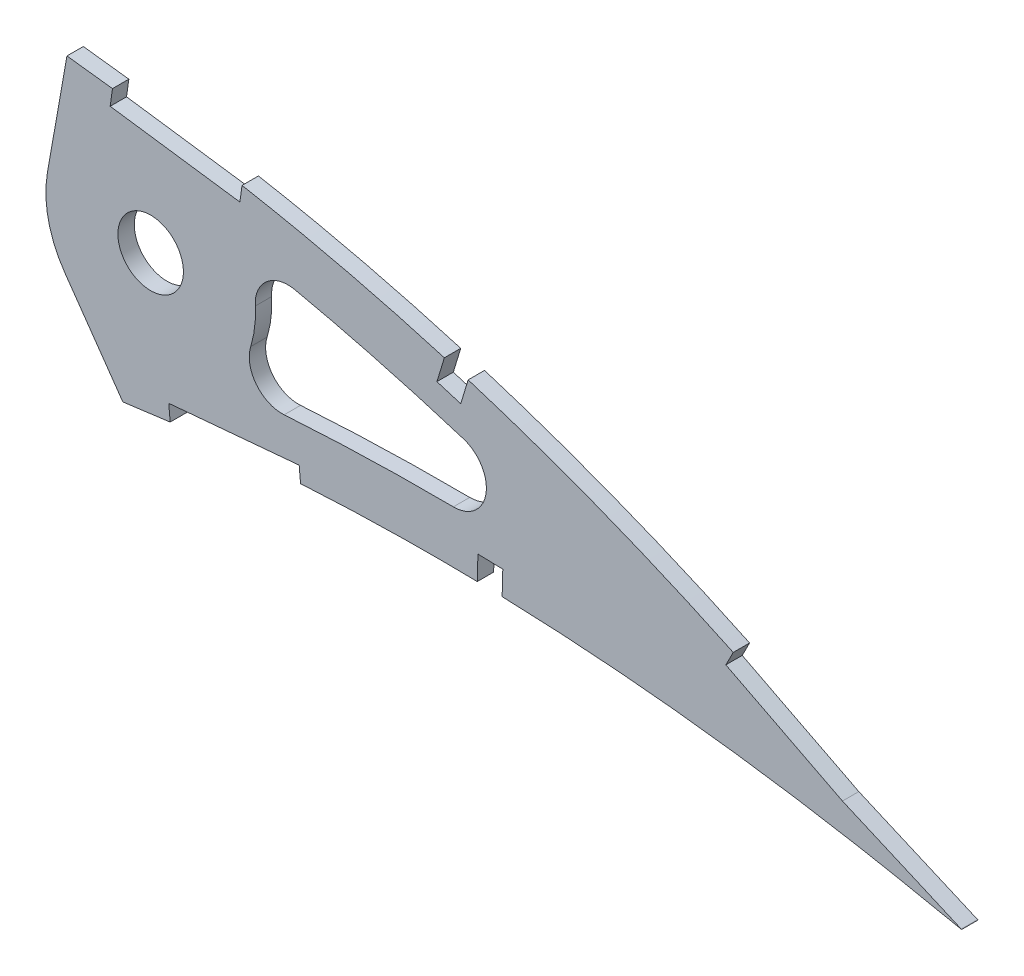
SolidWorks part; units mm, degrees
material "Plywood"
ref_plane "Front Plane" through (0, 0, 0) normal (0, 0, 1) x (1, 0, 0)
ref_plane "Top Plane" through (0, 0, 0) normal (0, 1, 0) x (1, 0, 0)
ref_plane "Right Plane" through (0, 0, 0) normal (1, 0, 0) x (0, 0, -1)
curve "Curve2"
  spline degree 3 poles (520.229, 0.8111, 0) (520.1892, 0.8357, 0) (520.0299, 0.9341, 0) (519.6711, 1.1542, 0) (519.0735, 1.5208, 0) (518.237, 2.0313, 0) (517.1622, 2.6844, 0) (515.8486, 3.4756, 0) (514.2969, 4.4021, 0) (512.5075, 5.4598, 0) (510.4807, 6.6436, 0) (508.2172, 7.9486, 0) (505.7172, 9.3676, 0) (502.9816, 10.8948, 0) (500.0114, 12.5227, 0) (496.8072, 14.2443, 0) (493.3701, 16.0505, 0) (489.7015, 17.9338, 0) (485.8019, 19.8836, 0) (481.6733, 21.8919, 0) (477.317, 23.9487, 0) (472.7345, 26.0429, 0) (467.9284, 28.1661, 0) (462.9001, 30.305, 0) (457.6524, 32.4505, 0) (452.1876, 34.5902, 0) (446.5089, 36.7144, 0) (440.6184, 38.8094, 0) (434.5207, 40.866, 0) (428.2186, 42.8708, 0) (421.7166, 44.813, 0) (415.0186, 46.68, 0) (408.1302, 48.4622, 0) (401.0555, 50.1466, 0) (393.8008, 51.7219, 0) (386.3718, 53.1787, 0) (378.7746, 54.5024, 0) (371.0303, 55.692, 0) (363.2636, 56.6815, 0) (355.5128, 57.652, 0) (347.7736, 58.5637, 0) (339.9398, 59.4368, 0) (332.019, 60.2663, 0) (324.019, 61.0497, 0) (315.9478, 61.7836, 0) (307.814, 62.4658, 0) (299.6253, 63.0925, 0) (291.3904, 63.6628, 0) (283.1174, 64.1714, 0) (274.8152, 64.6183, 0) (266.4922, 65.0001, 0) (258.157, 65.3142, 0) (249.8185, 65.5589, 0) (241.4854, 65.7316, 0) (233.1666, 65.8314, 0) (224.8708, 65.8555, 0) (216.6071, 65.8035, 0) (208.384, 65.6736, 0) (200.2107, 65.464, 0) (192.0958, 65.1743, 0) (184.048, 64.8046, 0) (176.0762, 64.3519, 0) (168.189, 63.8191, 0) (160.3952, 63.2038, 0) (152.7034, 62.506, 0) (145.1216, 61.7286, 0) (137.6583, 60.8693, 0) (130.3214, 59.9308, 0) (123.1191, 58.9147, 0) (116.0593, 57.8206, 0) (109.1496, 56.6517, 0) (102.3976, 55.409, 0) (95.8102, 54.0963, 0) (89.3948, 52.714, 0) (83.1581, 51.266, 0) (77.1065, 49.7551, 0) (71.2467, 48.1838, 0) (65.5845, 46.5561, 0) (60.1256, 44.8756, 0) (54.8764, 43.1442, 0) (49.8409, 41.3683, 0) (45.0253, 39.5493, 0) (40.4333, 37.6928, 0) (36.0702, 35.8014, 0) (31.9393, 33.8806, 0) (28.0452, 31.9329, 0) (24.3908, 29.9636, 0) (20.9797, 27.9757, 0) (17.8153, 25.973, 0) (14.8987, 23.9604, 0) (12.2341, 21.9394, 0) (9.8224, 19.9149, 0) (7.6651, 17.8901, 0) (5.7652, 15.8664, 0) (4.1228, 13.8473, 0) (2.7399, 11.8344, 0) (1.6168, 9.8297, 0) (0.7561, 7.8345, 0) (0.1568, 5.85, 0) (-0.1712, 3.8792, 0) (-0.2528, 1.9205, 0) (-0.0842, 0.6392, 0) (0, 0, 0) knots 0 0 0 0 0.000254 0.001015 0.002283 0.004057 0.006331 0.009105 0.012374 0.016134 0.02038 0.025106 0.030306 0.035972 0.0421 0.048678 0.055702 0.06316 0.071046 0.07935 0.088063 0.097176 0.106678 0.116562 0.126814 0.137428 0.148394 0.1597 0.171338 0.183298 0.19557 0.208144 0.221012 0.234162 0.247587 0.261277 0.275223 0.289414 0.303771 0.317689 0.331784 0.34604 0.360444 0.374983 0.38964 0.404403 0.419257 0.434187 0.449177 0.464215 0.479284 0.49437 0.509458 0.524532 0.539579 0.554583 0.56953 0.584403 0.599191 0.613877 0.628447 0.642889 0.657186 0.671326 0.685294 0.699078 0.712665 0.726043 0.739198 0.752118 0.764792 0.777208 0.789356 0.801224 0.812804 0.824083 0.835055 0.84571 0.856038 0.866034 0.875689 0.884998 0.893953 0.902553 0.910789 0.918661 0.926166 0.933303 0.940071 0.946475 0.952518 0.958205 0.963547 0.968557 0.97325 0.977651 0.981787 0.985694 0.989415 0.993001 0.996508 1 1 1 1
curve "Curve3"
  spline degree 3 poles (0, 0, 0) (0.1336, -0.6306, 0) (0.4014, -1.8948, 0) (1.129, -3.7148, 0) (2.0912, -5.4642, 0) (3.3081, -7.1386, 0) (4.7718, -8.7374, 0) (6.479, -10.2623, 0) (8.428, -11.7125, 0) (10.6162, -13.0874, 0) (13.0406, -14.3883, 0) (15.6982, -15.6145, 0) (18.5868, -16.7656, 0) (21.7032, -17.8401, 0) (25.0435, -18.8396, 0) (28.6046, -19.7616, 0) (32.3825, -20.6074, 0) (36.3735, -21.375, 0) (40.5732, -22.065, 0) (44.9774, -22.6771, 0) (49.5814, -23.2117, 0) (54.3808, -23.6676, 0) (59.3708, -24.0458, 0) (64.5464, -24.3466, 0) (69.9027, -24.5709, 0) (75.4344, -24.718, 0) (81.1363, -24.7899, 0) (87.003, -24.788, 0) (93.0289, -24.7115, 0) (99.2088, -24.5648, 0) (105.5368, -24.3469, 0) (112.0073, -24.0604, 0) (118.6142, -23.7083, 0) (125.3518, -23.2917, 0) (132.2141, -22.8125, 0) (139.1951, -22.2745, 0) (146.2885, -21.679, 0) (153.4882, -21.0296, 0) (160.7876, -20.3295, 0) (168.1806, -19.5808, 0) (175.6606, -18.7872, 0) (183.2209, -17.9512, 0) (190.8551, -17.0772, 0) (198.5563, -16.1668, 0) (206.3179, -15.2253, 0) (214.1326, -14.2544, 0) (221.9939, -13.2579, 0) (229.8947, -12.2404, 0) (237.8276, -11.2019, 0) (245.786, -10.1497, 0) (253.7621, -9.0829, 0) (261.7491, -8.0072, 0) (269.7395, -6.9257, 0) (277.7256, -5.8389, 0) (285.7003, -4.7513, 0) (293.6562, -3.6657, 0) (301.5856, -2.5824, 0) (309.4812, -1.5067, 0) (317.3352, -0.4385, 0) (325.1402, 0.6201, 0) (332.8888, 1.6659, 0) (340.5737, 2.6975, 0) (348.187, 3.7144, 0) (355.721, 4.7168, 0) (363.0553, 5.6745, 0) (370.1707, 6.6383, 0) (377.0913, 7.4284, 0) (383.9258, 8.1028, 0) (390.6811, 8.6557, 0) (397.3493, 9.0951, 0) (403.9227, 9.4241, 0) (410.3934, 9.6473, 0) (416.7532, 9.7713, 0) (422.9943, 9.7993, 0) (429.1081, 9.7402, 0) (435.0867, 9.5987, 0) (440.9216, 9.3813, 0) (446.6049, 9.0952, 0) (452.1283, 8.7483, 0) (457.4837, 8.3456, 0) (462.6634, 7.8966, 0) (467.6597, 7.4078, 0) (472.4647, 6.8849, 0) (477.0715, 6.3387, 0) (481.4727, 5.7729, 0) (485.6616, 5.1968, 0) (489.6316, 4.6162, 0) (493.3764, 4.0385, 0) (496.89, 3.4693, 0) (500.1667, 2.916, 0) (503.2016, 2.384, 0) (505.9892, 1.8782, 0) (508.5257, 1.4052, 0) (510.8062, 0.9673, 0) (512.8275, 0.5717, 0) (514.5859, 0.2202, 0) (516.0789, -0.0824, 0) (517.3037, -0.3347, 0) (518.2586, -0.5328, 0) (518.9417, -0.6767, 0) (519.3522, -0.7624, 0) (519.5346, -0.8013, 0) (519.5802, -0.8111, 0) knots 0 0 0 0 0.003638 0.007293 0.011028 0.014901 0.018963 0.023258 0.027821 0.032679 0.037853 0.043362 0.049215 0.055422 0.061989 0.068918 0.076211 0.083868 0.091887 0.100266 0.109 0.118085 0.127515 0.137285 0.147388 0.157816 0.168563 0.179619 0.190977 0.202627 0.21456 0.226767 0.239236 0.251959 0.264924 0.27812 0.291536 0.30516 0.318981 0.332985 0.347163 0.361499 0.375981 0.390597 0.405333 0.420175 0.43511 0.450124 0.465203 0.480333 0.495501 0.51069 0.525887 0.541078 0.556247 0.571382 0.586466 0.601485 0.616424 0.631269 0.646007 0.660621 0.675098 0.689423 0.703582 0.716908 0.730009 0.742952 0.755726 0.76832 0.780724 0.792927 0.804916 0.816679 0.828204 0.839475 0.850481 0.861208 0.871639 0.881763 0.891564 0.901027 0.910139 0.918884 0.927249 0.935221 0.942785 0.949928 0.956638 0.962904 0.968712 0.974054 0.978918 0.983297 0.98718 0.990561 0.993433 0.995791 0.99763 0.998946 0.999737 1 1 1 1
sketch "Sketch1" plane through (0, 0, 0) normal (0, 0, 1) x (1, 0, 0)
  line L1 (519.5802, -0.8111) -> (524.4049, -1.7687)
  line L2 (520.229, 0.8111) -> (524.4049, -1.7687)
  spline S0 degree 3 poles (-2903.7635, -749.124) (66.2436, 68.8235) (-8.6937, 20.855) (1.129, -3.7148) (2.0912, -5.4642) (3.3081, -7.1386) (4.7718, -8.7374) (6.479, -10.2623) (8.428, -11.7125) (10.6162, -13.0874) (13.0406, -14.3883) (15.6982, -15.6145) (18.5868, -16.7656) (21.7032, -17.8401) (25.0435, -18.8396) (28.6046, -19.7616) (32.3825, -20.6074) (36.3735, -21.375) (40.5732, -22.065) (44.9774, -22.6771) (49.5814, -23.2117) (54.3808, -23.6676) (59.3708, -24.0458) (64.5464, -24.3466) (69.9027, -24.5709) (75.4344, -24.718) (81.1363, -24.7899) (87.003, -24.788) (93.0289, -24.7115) (99.2088, -24.5648) (105.5368, -24.3469) (112.0073, -24.0604) (118.6142, -23.7083) (125.3518, -23.2917) (132.2141, -22.8125) (139.1951, -22.2745) (146.2885, -21.679) (153.4882, -21.0296) (160.7876, -20.3295) (168.1806, -19.5808) (175.6606, -18.7872) (183.2209, -17.9512) (190.8551, -17.0772) (198.5563, -16.1668) (206.3179, -15.2253) (214.1326, -14.2544) (221.9939, -13.2579) (229.8947, -12.2404) (237.8276, -11.2019) (245.786, -10.1497) (253.7621, -9.0829) (261.7491, -8.0072) (269.7395, -6.9257) (277.7256, -5.8389) (285.7003, -4.7513) (293.6562, -3.6657) (301.5856, -2.5824) (309.4812, -1.5067) (317.3352, -0.4385) (325.1402, 0.6201) (332.8888, 1.6659) (340.5737, 2.6975) (348.187, 3.7144) (355.721, 4.7168) (363.0553, 5.6745) (370.1707, 6.6383) (377.0913, 7.4284) (383.9258, 8.1028) (390.6811, 8.6557) (397.3493, 9.0951) (403.9227, 9.4241) (410.3934, 9.6473) (416.7532, 9.7713) (422.9943, 9.7993) (429.1081, 9.7402) (435.0867, 9.5987) (440.9216, 9.3813) (446.6049, 9.0952) (452.1283, 8.7483) (457.4837, 8.3456) (462.6634, 7.8966) (467.6597, 7.4078) (472.4647, 6.8849) (477.0715, 6.3387) (481.4727, 5.7729) (485.6616, 5.1968) (489.6316, 4.6162) (493.3764, 4.0385) (496.89, 3.4693) (500.1667, 2.916) (503.2016, 2.384) (505.9892, 1.8782) (508.5257, 1.4052) (510.8062, 0.9673) (512.8275, 0.5717) (514.5859, 0.2202) (516.0789, -0.0824) (517.3037, -0.3347) (518.2586, -0.5328) (518.9417, -0.6767) (537.0698, -4.4604) (553.3394, -15.9066) (1193.1482, 2921.6684) knots -0.137857 -0.137857 -0.137857 -0.137857 0.003638 0.007293 0.011028 0.014901 0.018963 0.023258 0.027821 0.032679 0.037853 0.043362 0.049215 0.055422 0.061989 0.068918 0.076211 0.083868 0.091887 0.100266 0.109 0.118085 0.127515 0.137285 0.147388 0.157816 0.168563 0.179619 0.190977 0.202627 0.21456 0.226767 0.239236 0.251959 0.264924 0.27812 0.291536 0.30516 0.318981 0.332985 0.347163 0.361499 0.375981 0.390597 0.405333 0.420175 0.43511 0.450124 0.465203 0.480333 0.495501 0.51069 0.525887 0.541078 0.556247 0.571382 0.586466 0.601485 0.616424 0.631269 0.646007 0.660621 0.675098 0.689423 0.703582 0.716908 0.730009 0.742952 0.755726 0.76832 0.780724 0.792927 0.804916 0.816679 0.828204 0.839475 0.850481 0.861208 0.871639 0.881763 0.891564 0.901027 0.910139 0.918884 0.927249 0.935221 0.942785 0.949928 0.956638 0.962904 0.968712 0.974054 0.978918 0.983297 0.98718 0.990561 0.993433 0.995791 0.99763 0.998946 0.999737 1.102307 1.102307 1.102307 1.102307 only from (0, 0) to (519.5802, -0.8111) construction
  spline S1 degree 3 poles (2144.5607, 2521.6799) (550.9976, -26.3511) (537.2872, -9.6513) (519.6711, 1.1542) (519.0735, 1.5208) (518.237, 2.0313) (517.1622, 2.6844) (515.8486, 3.4756) (514.2969, 4.4021) (512.5075, 5.4598) (510.4807, 6.6436) (508.2172, 7.9486) (505.7172, 9.3676) (502.9816, 10.8948) (500.0114, 12.5227) (496.8072, 14.2443) (493.3701, 16.0505) (489.7015, 17.9338) (485.8019, 19.8836) (481.6733, 21.8919) (477.317, 23.9487) (472.7345, 26.0429) (467.9284, 28.1661) (462.9001, 30.305) (457.6524, 32.4505) (452.1876, 34.5902) (446.5089, 36.7144) (440.6184, 38.8094) (434.5207, 40.866) (428.2186, 42.8708) (421.7166, 44.813) (415.0186, 46.68) (408.1302, 48.4622) (401.0555, 50.1466) (393.8008, 51.7219) (386.3718, 53.1787) (378.7746, 54.5024) (371.0303, 55.692) (363.2636, 56.6815) (355.5128, 57.652) (347.7736, 58.5637) (339.9398, 59.4368) (332.019, 60.2663) (324.019, 61.0497) (315.9478, 61.7836) (307.814, 62.4658) (299.6253, 63.0925) (291.3904, 63.6628) (283.1174, 64.1714) (274.8152, 64.6183) (266.4922, 65.0001) (258.157, 65.3142) (249.8185, 65.5589) (241.4854, 65.7316) (233.1666, 65.8314) (224.8708, 65.8555) (216.6071, 65.8035) (208.384, 65.6736) (200.2107, 65.464) (192.0958, 65.1743) (184.048, 64.8046) (176.0762, 64.3519) (168.189, 63.8191) (160.3952, 63.2038) (152.7034, 62.506) (145.1216, 61.7286) (137.6583, 60.8693) (130.3214, 59.9308) (123.1191, 58.9147) (116.0593, 57.8206) (109.1496, 56.6517) (102.3976, 55.409) (95.8102, 54.0963) (89.3948, 52.714) (83.1581, 51.266) (77.1065, 49.7551) (71.2467, 48.1838) (65.5845, 46.5561) (60.1256, 44.8756) (54.8764, 43.1442) (49.8409, 41.3683) (45.0253, 39.5493) (40.4333, 37.6928) (36.0702, 35.8014) (31.9393, 33.8806) (28.0452, 31.9329) (24.3908, 29.9636) (20.9797, 27.9757) (17.8153, 25.973) (14.8987, 23.9604) (12.2341, 21.9394) (9.8224, 19.9149) (7.6651, 17.8901) (5.7652, 15.8664) (4.1228, 13.8473) (2.7399, 11.8344) (1.6168, 9.8297) (0.7561, 7.8345) (0.1568, 5.85) (-0.1712, 3.8792) (-1.2714, -22.5145) (85.5395, -42.7616) (-2987.8188, -259.5241) knots -0.109813 -0.109813 -0.109813 -0.109813 0.000254 0.001015 0.002283 0.004057 0.006331 0.009105 0.012374 0.016134 0.02038 0.025106 0.030306 0.035972 0.0421 0.048678 0.055702 0.06316 0.071046 0.07935 0.088063 0.097176 0.106678 0.116562 0.126814 0.137428 0.148394 0.1597 0.171338 0.183298 0.19557 0.208144 0.221012 0.234162 0.247587 0.261277 0.275223 0.289414 0.303771 0.317689 0.331784 0.34604 0.360444 0.374983 0.38964 0.404403 0.419257 0.434187 0.449177 0.464215 0.479284 0.49437 0.509458 0.524532 0.539579 0.554583 0.56953 0.584403 0.599191 0.613877 0.628447 0.642889 0.657186 0.671326 0.685294 0.699078 0.712665 0.726043 0.739198 0.752118 0.764792 0.777208 0.789356 0.801224 0.812804 0.824083 0.835055 0.84571 0.856038 0.866034 0.875689 0.884998 0.893953 0.902553 0.910789 0.918661 0.926166 0.933303 0.940071 0.946475 0.952518 0.958205 0.963547 0.968557 0.97325 0.977651 0.981787 0.985694 0.989415 0.993001 0.996508 1.132043 1.132043 1.132043 1.132043 only from (520.229, 0.8111) to (0, 0) construction
  spline S2 degree 3 poles (0, 0) (0.1336, -0.6306) (0.4014, -1.8948) (1.129, -3.7148) (2.0912, -5.4642) (3.3081, -7.1386) (4.7718, -8.7374) (6.479, -10.2623) (8.428, -11.7125) (10.6162, -13.0874) (13.0406, -14.3883) (15.6982, -15.6145) (18.5868, -16.7656) (21.7032, -17.8401) (25.0435, -18.8396) (28.6046, -19.7616) (32.3825, -20.6074) (36.3735, -21.375) (40.5732, -22.065) (44.9774, -22.6771) (49.5814, -23.2117) (54.3808, -23.6676) (59.3708, -24.0458) (64.5464, -24.3466) (69.9027, -24.5709) (75.4344, -24.718) (81.1363, -24.7899) (87.003, -24.788) (93.0289, -24.7115) (99.2088, -24.5648) (105.5368, -24.3469) (112.0073, -24.0604) (118.6142, -23.7083) (125.3518, -23.2917) (132.2141, -22.8125) (139.1951, -22.2745) (146.2885, -21.679) (153.4882, -21.0296) (160.7876, -20.3295) (168.1806, -19.5808) (175.6606, -18.7872) (183.2209, -17.9512) (190.8551, -17.0772) (198.5563, -16.1668) (206.3179, -15.2253) (214.1326, -14.2544) (221.9939, -13.2579) (229.8947, -12.2404) (237.8276, -11.2019) (245.786, -10.1497) (253.7621, -9.0829) (261.7491, -8.0072) (269.7395, -6.9257) (277.7256, -5.8389) (285.7003, -4.7513) (293.6562, -3.6657) (301.5856, -2.5824) (309.4812, -1.5067) (317.3352, -0.4385) (325.1402, 0.6201) (332.8888, 1.6659) (340.5737, 2.6975) (348.187, 3.7144) (355.721, 4.7168) (363.0553, 5.6745) (370.1707, 6.6383) (377.0913, 7.4284) (383.9258, 8.1028) (390.6811, 8.6557) (397.3493, 9.0951) (403.9227, 9.4241) (410.3934, 9.6473) (416.7532, 9.7713) (422.9943, 9.7993) (429.1081, 9.7402) (435.0867, 9.5987) (440.9216, 9.3813) (446.6049, 9.0952) (452.1283, 8.7483) (457.4837, 8.3456) (462.6634, 7.8966) (467.6597, 7.4078) (472.4647, 6.8849) (477.0715, 6.3387) (481.4727, 5.7729) (485.6616, 5.1968) (489.6316, 4.6162) (493.3764, 4.0385) (496.89, 3.4693) (500.1667, 2.916) (503.2016, 2.384) (505.9892, 1.8782) (508.5257, 1.4052) (510.8062, 0.9673) (512.8275, 0.5717) (514.5859, 0.2202) (516.0789, -0.0824) (517.3037, -0.3347) (518.2586, -0.5328) (518.9417, -0.6767) (519.3522, -0.7624) (519.5346, -0.8013) (519.5802, -0.8111) knots 0 0 0 0 0.003638 0.007293 0.011028 0.014901 0.018963 0.023258 0.027821 0.032679 0.037853 0.043362 0.049215 0.055422 0.061989 0.068918 0.076211 0.083868 0.091887 0.100266 0.109 0.118085 0.127515 0.137285 0.147388 0.157816 0.168563 0.179619 0.190977 0.202627 0.21456 0.226767 0.239236 0.251959 0.264924 0.27812 0.291536 0.30516 0.318981 0.332985 0.347163 0.361499 0.375981 0.390597 0.405333 0.420175 0.43511 0.450124 0.465203 0.480333 0.495501 0.51069 0.525887 0.541078 0.556247 0.571382 0.586466 0.601485 0.616424 0.631269 0.646007 0.660621 0.675098 0.689423 0.703582 0.716908 0.730009 0.742952 0.755726 0.76832 0.780724 0.792927 0.804916 0.816679 0.828204 0.839475 0.850481 0.861208 0.871639 0.881763 0.891564 0.901027 0.910139 0.918884 0.927249 0.935221 0.942785 0.949928 0.956638 0.962904 0.968712 0.974054 0.978918 0.983297 0.98718 0.990561 0.993433 0.995791 0.99763 0.998946 0.999737 1 1 1 1
  spline S3 degree 3 poles (520.229, 0.8111) (520.1892, 0.8357) (520.0299, 0.9341) (519.6711, 1.1542) (519.0735, 1.5208) (518.237, 2.0313) (517.1622, 2.6844) (515.8486, 3.4756) (514.2969, 4.4021) (512.5075, 5.4598) (510.4807, 6.6436) (508.2172, 7.9486) (505.7172, 9.3676) (502.9816, 10.8948) (500.0114, 12.5227) (496.8072, 14.2443) (493.3701, 16.0505) (489.7015, 17.9338) (485.8019, 19.8836) (481.6733, 21.8919) (477.317, 23.9487) (472.7345, 26.0429) (467.9284, 28.1661) (462.9001, 30.305) (457.6524, 32.4505) (452.1876, 34.5902) (446.5089, 36.7144) (440.6184, 38.8094) (434.5207, 40.866) (428.2186, 42.8708) (421.7166, 44.813) (415.0186, 46.68) (408.1302, 48.4622) (401.0555, 50.1466) (393.8008, 51.7219) (386.3718, 53.1787) (378.7746, 54.5024) (371.0303, 55.692) (363.2636, 56.6815) (355.5128, 57.652) (347.7736, 58.5637) (339.9398, 59.4368) (332.019, 60.2663) (324.019, 61.0497) (315.9478, 61.7836) (307.814, 62.4658) (299.6253, 63.0925) (291.3904, 63.6628) (283.1174, 64.1714) (274.8152, 64.6183) (266.4922, 65.0001) (258.157, 65.3142) (249.8185, 65.5589) (241.4854, 65.7316) (233.1666, 65.8314) (224.8708, 65.8555) (216.6071, 65.8035) (208.384, 65.6736) (200.2107, 65.464) (192.0958, 65.1743) (184.048, 64.8046) (176.0762, 64.3519) (168.189, 63.8191) (160.3952, 63.2038) (152.7034, 62.506) (145.1216, 61.7286) (137.6583, 60.8693) (130.3214, 59.9308) (123.1191, 58.9147) (116.0593, 57.8206) (109.1496, 56.6517) (102.3976, 55.409) (95.8102, 54.0963) (89.3948, 52.714) (83.1581, 51.266) (77.1065, 49.7551) (71.2467, 48.1838) (65.5845, 46.5561) (60.1256, 44.8756) (54.8764, 43.1442) (49.8409, 41.3683) (45.0253, 39.5493) (40.4333, 37.6928) (36.0702, 35.8014) (31.9393, 33.8806) (28.0452, 31.9329) (24.3908, 29.9636) (20.9797, 27.9757) (17.8153, 25.973) (14.8987, 23.9604) (12.2341, 21.9394) (9.8224, 19.9149) (7.6651, 17.8901) (5.7652, 15.8664) (4.1228, 13.8473) (2.7399, 11.8344) (1.6168, 9.8297) (0.7561, 7.8345) (0.1568, 5.85) (-0.1712, 3.8792) (-0.2528, 1.9205) (-0.0842, 0.6392) (0, 0) knots 0 0 0 0 0.000254 0.001015 0.002283 0.004057 0.006331 0.009105 0.012374 0.016134 0.02038 0.025106 0.030306 0.035972 0.0421 0.048678 0.055702 0.06316 0.071046 0.07935 0.088063 0.097176 0.106678 0.116562 0.126814 0.137428 0.148394 0.1597 0.171338 0.183298 0.19557 0.208144 0.221012 0.234162 0.247587 0.261277 0.275223 0.289414 0.303771 0.317689 0.331784 0.34604 0.360444 0.374983 0.38964 0.404403 0.419257 0.434187 0.449177 0.464215 0.479284 0.49437 0.509458 0.524532 0.539579 0.554583 0.56953 0.584403 0.599191 0.613877 0.628447 0.642889 0.657186 0.671326 0.685294 0.699078 0.712665 0.726043 0.739198 0.752118 0.764792 0.777208 0.789356 0.801224 0.812804 0.824083 0.835055 0.84571 0.856038 0.866034 0.875689 0.884998 0.893953 0.902553 0.910789 0.918661 0.926166 0.933303 0.940071 0.946475 0.952518 0.958205 0.963547 0.968557 0.97325 0.977651 0.981787 0.985694 0.989415 0.993001 0.996508 1 1 1 1
extrude "Boss-Extrude1" add sketch "Sketch1" along normal blind 3.175
sketch "Sketch4" plane through (0, 0, 0) normal (0, 0, -1) x (-1, 0, 0)
  line L0 (-347.1309, 36.7611) -> (-350.9097, 58.1919)
  line L1 (-350.497, 21.5775) -> (-361.7496, 5.5072)
  line L2 (-367.1422, 33.2326) -> (-406.863, 33.2326)
  circle A0 centre (-367.1422, 33.2326) radius 20.32
  circle A1 centre (-367.1422, 33.2326) radius 6.35
  spline S2 degree 3 poles (1939.7558, -484.7932) (-49.4812, 57.6608) (7.5449, 17.9816) (-1.129, -3.7148) (-2.0912, -5.4642) (-3.3081, -7.1386) (-4.7718, -8.7374) (-6.479, -10.2623) (-8.428, -11.7125) (-10.6162, -13.0874) (-13.0406, -14.3883) (-15.6982, -15.6145) (-18.5868, -16.7656) (-21.7032, -17.8401) (-25.0435, -18.8396) (-28.6046, -19.7616) (-32.3825, -20.6074) (-36.3735, -21.375) (-40.5732, -22.065) (-44.9774, -22.6771) (-49.5814, -23.2117) (-54.3808, -23.6676) (-59.3708, -24.0458) (-64.5464, -24.3466) (-69.9027, -24.5709) (-75.4344, -24.718) (-81.1363, -24.7899) (-87.003, -24.788) (-93.0289, -24.7115) (-99.2088, -24.5648) (-105.5368, -24.3469) (-112.0073, -24.0604) (-118.6142, -23.7083) (-125.3518, -23.2917) (-132.2141, -22.8125) (-139.1951, -22.2745) (-146.2885, -21.679) (-153.4882, -21.0296) (-160.7876, -20.3295) (-168.1806, -19.5808) (-175.6606, -18.7872) (-183.2209, -17.9512) (-190.8551, -17.0772) (-198.5563, -16.1668) (-206.3179, -15.2253) (-214.1326, -14.2544) (-221.9939, -13.2579) (-229.8947, -12.2404) (-237.8276, -11.2019) (-245.786, -10.1497) (-253.7621, -9.0829) (-261.7491, -8.0072) (-269.7395, -6.9257) (-277.7256, -5.8389) (-285.7003, -4.7513) (-293.6562, -3.6657) (-301.5856, -2.5824) (-309.4812, -1.5067) (-317.3352, -0.4385) (-325.1402, 0.6201) (-332.8888, 1.6659) (-340.5737, 2.6975) (-348.187, 3.7144) (-355.721, 4.7168) (-363.0553, 5.6745) (-370.1707, 6.6383) (-377.0913, 7.4284) (-383.9258, 8.1028) (-390.6811, 8.6557) (-397.3493, 9.0951) (-403.9227, 9.4241) (-410.3934, 9.6473) (-416.7532, 9.7713) (-422.9943, 9.7993) (-429.1081, 9.7402) (-435.0867, 9.5987) (-440.9216, 9.3813) (-446.6049, 9.0952) (-452.1283, 8.7483) (-457.4837, 8.3456) (-462.6634, 7.8966) (-467.6597, 7.4078) (-472.4647, 6.8849) (-477.0715, 6.3387) (-481.4727, 5.7729) (-485.6616, 5.1968) (-489.6316, 4.6162) (-493.3764, 4.0385) (-496.89, 3.4693) (-500.1667, 2.916) (-503.2016, 2.384) (-505.9892, 1.8782) (-508.5257, 1.4052) (-510.8062, 0.9673) (-512.8275, 0.5717) (-514.5859, 0.2202) (-516.0789, -0.0824) (-517.3037, -0.3347) (-518.2586, -0.5328) (-518.9417, -0.6767) (-534.8295, -3.9928) (-549.2415, -13.1623) (-979.5797, 1945.0117) knots -0.120445 -0.120445 -0.120445 -0.120445 0.003638 0.007293 0.011028 0.014901 0.018963 0.023258 0.027821 0.032679 0.037853 0.043362 0.049215 0.055422 0.061989 0.068918 0.076211 0.083868 0.091887 0.100266 0.109 0.118085 0.127515 0.137285 0.147388 0.157816 0.168563 0.179619 0.190977 0.202627 0.21456 0.226767 0.239236 0.251959 0.264924 0.27812 0.291536 0.30516 0.318981 0.332985 0.347163 0.361499 0.375981 0.390597 0.405333 0.420175 0.43511 0.450124 0.465203 0.480333 0.495501 0.51069 0.525887 0.541078 0.556247 0.571382 0.586466 0.601485 0.616424 0.631269 0.646007 0.660621 0.675098 0.689423 0.703582 0.716908 0.730009 0.742952 0.755726 0.76832 0.780724 0.792927 0.804916 0.816679 0.828204 0.839475 0.850481 0.861208 0.871639 0.881763 0.891564 0.901027 0.910139 0.918884 0.927249 0.935221 0.942785 0.949928 0.956638 0.962904 0.968712 0.974054 0.978918 0.983297 0.98718 0.990561 0.993433 0.995791 0.99763 0.998946 0.999737 1.089371 1.089371 1.089371 1.089371 only from (0, 0) to (-519.5802, -0.8111) construction
  spline S3 degree 3 poles (-1613.7482, 1674.6901) (-547.5042, -22.2613) (-535.1053, -8.313) (-519.6711, 1.1542) (-519.0735, 1.5208) (-518.237, 2.0313) (-517.1622, 2.6844) (-515.8486, 3.4756) (-514.2969, 4.4021) (-512.5075, 5.4598) (-510.4807, 6.6436) (-508.2172, 7.9486) (-505.7172, 9.3676) (-502.9816, 10.8948) (-500.0114, 12.5227) (-496.8072, 14.2443) (-493.3701, 16.0505) (-489.7015, 17.9338) (-485.8019, 19.8836) (-481.6733, 21.8919) (-477.317, 23.9487) (-472.7345, 26.0429) (-467.9284, 28.1661) (-462.9001, 30.305) (-457.6524, 32.4505) (-452.1876, 34.5902) (-446.5089, 36.7144) (-440.6184, 38.8094) (-434.5207, 40.866) (-428.2186, 42.8708) (-421.7166, 44.813) (-415.0186, 46.68) (-408.1302, 48.4622) (-401.0555, 50.1466) (-393.8008, 51.7219) (-386.3718, 53.1787) (-378.7746, 54.5024) (-371.0303, 55.692) (-363.2636, 56.6815) (-355.5128, 57.652) (-347.7736, 58.5637) (-339.9398, 59.4368) (-332.019, 60.2663) (-324.019, 61.0497) (-315.9478, 61.7836) (-307.814, 62.4658) (-299.6253, 63.0925) (-291.3904, 63.6628) (-283.1174, 64.1714) (-274.8152, 64.6183) (-266.4922, 65.0001) (-258.157, 65.3142) (-249.8185, 65.5589) (-241.4854, 65.7316) (-233.1666, 65.8314) (-224.8708, 65.8555) (-216.6071, 65.8035) (-208.384, 65.6736) (-200.2107, 65.464) (-192.0958, 65.1743) (-184.048, 64.8046) (-176.0762, 64.3519) (-168.189, 63.8191) (-160.3952, 63.2038) (-152.7034, 62.506) (-145.1216, 61.7286) (-137.6583, 60.8693) (-130.3214, 59.9308) (-123.1191, 58.9147) (-116.0593, 57.8206) (-109.1496, 56.6517) (-102.3976, 55.409) (-95.8102, 54.0963) (-89.3948, 52.714) (-83.1581, 51.266) (-77.1065, 49.7551) (-71.2467, 48.1838) (-65.5845, 46.5561) (-60.1256, 44.8756) (-54.8764, 43.1442) (-49.8409, 41.3683) (-45.0253, 39.5493) (-40.4333, 37.6928) (-36.0702, 35.8014) (-31.9393, 33.8806) (-28.0452, 31.9329) (-24.3908, 29.9636) (-20.9797, 27.9757) (-17.8153, 25.973) (-14.8987, 23.9604) (-12.2341, 21.9394) (-9.8224, 19.9149) (-7.6651, 17.8901) (-5.7652, 15.8664) (-4.1228, 13.8473) (-2.7399, 11.8344) (-1.6168, 9.8297) (-0.7561, 7.8345) (-0.1568, 5.85) (0.1712, 3.8792) (1.1427, -19.4272) (-65.9725, -37.8239) (1990.4087, -188.0581) knots -0.095928 -0.095928 -0.095928 -0.095928 0.000254 0.001015 0.002283 0.004057 0.006331 0.009105 0.012374 0.016134 0.02038 0.025106 0.030306 0.035972 0.0421 0.048678 0.055702 0.06316 0.071046 0.07935 0.088063 0.097176 0.106678 0.116562 0.126814 0.137428 0.148394 0.1597 0.171338 0.183298 0.19557 0.208144 0.221012 0.234162 0.247587 0.261277 0.275223 0.289414 0.303771 0.317689 0.331784 0.34604 0.360444 0.374983 0.38964 0.404403 0.419257 0.434187 0.449177 0.464215 0.479284 0.49437 0.509458 0.524532 0.539579 0.554583 0.56953 0.584403 0.599191 0.613877 0.628447 0.642889 0.657186 0.671326 0.685294 0.699078 0.712665 0.726043 0.739198 0.752118 0.764792 0.777208 0.789356 0.801224 0.812804 0.824083 0.835055 0.84571 0.856038 0.866034 0.875689 0.884998 0.893953 0.902553 0.910789 0.918661 0.926166 0.933303 0.940071 0.946475 0.952518 0.958205 0.963547 0.968557 0.97325 0.977651 0.981787 0.985694 0.989415 0.993001 0.996508 1.11536 1.11536 1.11536 1.11536 only from (-520.229, 0.8111) to (0, 0) construction
  spline S4 degree 3 poles (-1978.354, 2157.5892) (159.6529, 858.6126) (-7.0413, 13.2519) (-10.1565, 1.1414) (-10.167, 1.1042) (-10.1763, 1.0725) (-10.1781, 1.0668) (-10.1835, 1.0497) (-10.1867, 1.0399) (-10.2052, 0.985) (-10.2286, 0.9219) (-10.2791, 0.8017) (-10.2985, 0.7574) (-10.3426, 0.661) (-10.3676, 0.6085) (-10.4428, 0.4561) (-10.496, 0.3558) (-10.6081, 0.1584) (-10.6662, 0.0627) (-10.855, -0.2291) (-11.0064, -0.4384) (-11.5378, -1.0936) (-11.9971, -1.5677) (-13.099, -2.5256) (-13.7412, -3.01) (-15.1702, -3.9568) (-15.9588, -4.4208) (-17.636, -5.3094) (-18.5262, -5.7351) (-21.3094, -6.9503) (-23.3073, -7.6749) (-27.467, -8.9758) (-29.6229, -9.5497) (-34.0316, -10.5753) (-36.2795, -11.0252) (-40.839, -11.8243) (-43.1471, -12.1728) (-47.8035, -12.7862) (-50.1501, -13.0508) (-57.2292, -13.7373) (-62.003, -14.0541) (-71.5985, -14.4809) (-76.422, -14.5891) (-83.6816, -14.6324) (-86.1037, -14.6268) (-90.9551, -14.5789) (-93.3856, -14.5371) (-100.6793, -14.3647) (-105.548, -14.1854) (-120.1773, -13.4939) (-129.9476, -12.83) (-149.5009, -11.2301) (-159.287, -10.2936) (-178.863, -8.2392) (-188.6532, -7.1203) (-203.3458, -5.3542) (-208.2424, -4.7511) (-218.0387, -3.5207) (-222.9395, -2.8943) (-232.7359, -1.6243) (-237.6385, -0.9795) (-247.4393, 0.3202) (-252.3404, 0.9774) (-262.147, 2.2986) (-267.05, 2.9625) (-276.8577, 4.2964) (-281.7641, 4.9659) (-291.5768, 6.3047) (-296.4825, 6.9752) (-306.3007, 8.3142) (-311.2087, 8.9822) (-325.9378, 10.9826) (-335.766, 12.3068) (-348.0467, 13.9451) (-350.5039, 14.2725) (-354.1964, 14.7609) (-355.4285, 14.923) (-357.8843, 15.2457) (-359.1092, 15.4066) (-361.5526, 15.7296) (-362.7689, 15.8922) (-365.2348, 16.221) (-366.4798, 16.3859) (-368.3663, 16.6273) (-368.9995, 16.7068) (-371.53, 17.0174) (-373.424, 17.2342) (-377.8329, 17.7104) (-380.3527, 17.9617) (-385.4072, 18.4196) (-387.9354, 18.6255) (-395.5221, 19.1767) (-400.5883, 19.4552) (-408.19, 19.7386) (-410.7237, 19.8108) (-415.7936, 19.9113) (-418.3301, 19.9392) (-425.9339, 19.9566) (-431.0019, 19.8815) (-441.1324, 19.5579) (-446.1907, 19.3102) (-453.7725, 18.8139) (-456.2982, 18.6271) (-775.6257, -7.5609) (-1062.3017, -351.5368) (-2984.1092, -1609.9578) knots -0.216436 -0.216436 -0.216436 -0.216436 0.001953 0.001953 0.00293 0.00293 0.003418 0.003418 0.003906 0.003906 0.005859 0.005859 0.006836 0.006836 0.007813 0.007813 0.009766 0.009766 0.011719 0.011719 0.015625 0.015625 0.023438 0.023438 0.03125 0.03125 0.039063 0.039063 0.046875 0.046875 0.0625 0.0625 0.078125 0.078125 0.09375 0.09375 0.109375 0.109375 0.125 0.125 0.15625 0.15625 0.1875 0.1875 0.203125 0.203125 0.21875 0.21875 0.25 0.25 0.3125 0.3125 0.375 0.375 0.4375 0.4375 0.46875 0.46875 0.5 0.5 0.53125 0.53125 0.5625 0.5625 0.59375 0.59375 0.625 0.625 0.65625 0.65625 0.6875 0.6875 0.75 0.75 0.765625 0.765625 0.773438 0.773438 0.78125 0.78125 0.789063 0.789063 0.796875 0.796875 0.800781 0.800781 0.8125 0.8125 0.828125 0.828125 0.84375 0.84375 0.875 0.875 0.890625 0.890625 0.90625 0.90625 0.9375 0.9375 0.96875 0.96875 0.984375 0.984375 2.947098 2.947098 2.947098 2.947098 only from (-10.022, 1.7185) to (-466.3815, 17.739)
  spline S5 degree 3 poles (-2960.1923, -1647.6146) (-778.0163, -316.2747) (-661.2066, -63.7231) (-457.1185, 21.6971) (-454.7864, 22.6463) (-450.1039, 24.4978) (-447.7524, 25.4007) (-443.0352, 27.1579) (-440.669, 28.0121) (-428.7885, 32.1652) (-419.1573, 35.0991) (-404.5516, 38.8923) (-399.6593, 40.0545) (-392.2853, 41.6432) (-389.8214, 42.1473) (-384.8862, 43.1026) (-382.4148, 43.5535) (-377.456, 44.4051) (-374.9691, 44.8071) (-371.8706, 45.272) (-371.2512, 45.3631) (-370.0129, 45.5414) (-369.3949, 45.6283) (-367.531, 45.885) (-365.6514, 46.1331) (-363.7495, 46.3759) (-362.4766, 46.5374) (-361.8369, 46.6182) (-359.9197, 46.8599) (-358.6437, 47.0199) (-354.8218, 47.4941) (-352.2828, 47.8012) (-347.1922, 48.3982) (-344.6438, 48.6888) (-339.5477, 49.2537) (-336.9993, 49.5279) (-329.3512, 50.3256) (-324.2496, 50.8242) (-308.9368, 52.2174) (-298.7176, 53.0107) (-278.2717, 54.3039) (-268.0406, 54.8057) (-247.5801, 55.4913) (-237.3501, 55.6755) (-216.9004, 55.6922) (-206.6831, 55.5256) (-191.3779, 54.9785) (-186.2812, 54.7472) (-176.0979, 54.177) (-171.0099, 53.8396) (-160.8533, 53.0504) (-155.7814, 52.598) (-145.6574, 51.572) (-140.6072, 50.9971) (-125.4892, 49.071) (-115.4646, 47.5214) (-100.5547, 44.7064) (-95.6096, 43.687) (-85.777, 41.462) (-80.8922, 40.2578) (-71.2072, 37.6367) (-66.4068, 36.2209) (-59.3024, 33.909) (-56.9474, 33.1063) (-52.2821, 31.4343) (-49.9693, 30.5636) (-45.3927, 28.7458) (-43.1318, 27.7996) (-38.6715, 25.8196) (-36.476, 24.7882) (-32.1758, 22.6281) (-30.0692, 21.4995) (-27.0125, 19.7284) (-26.0103, 19.1247) (-24.0464, 17.889) (-23.0831, 17.2561) (-21.2128, 15.9659) (-20.3049, 15.3076) (-18.5534, 13.9629) (-17.7093, 13.2763) (-16.1081, 11.8824) (-15.3519, 11.176) (-14.3045, 10.1109) (-13.9701, 9.7552) (-13.3325, 9.0431) (-13.0296, 8.687) (-12.1803, 7.6299) (-11.6896, 6.9348) (-10.8906, 5.6128) (-10.5874, 4.9936) (-10.269, 4.158) (-10.1861, 3.8969) (-10.0953, 3.5459) (-10.0707, 3.4366) (-10.0267, 3.2104) (-10.0081, 3.096) (-9.9777, 2.8649) (-9.9658, 2.7438) (-9.9529, 2.5547) (-9.9512, 2.4811) (-9.9516, 2.4178) (-9.9518, 2.4066) (-9.9523, 2.387) (-9.9526, 2.38) (-9.9538, 2.3538) (-9.956, 2.318) (-10.9137, -8.9231) (-124.2495, -805.3826) (-2616.8841, -1329.8892) knots -1.341255 -1.341255 -1.341255 -1.341255 0.015625 0.015625 0.03125 0.03125 0.046875 0.046875 0.0625 0.0625 0.125 0.125 0.15625 0.15625 0.171875 0.171875 0.1875 0.1875 0.203125 0.203125 0.207031 0.207031 0.210937 0.210937 0.21875 0.222656 0.222656 0.226562 0.226562 0.234375 0.234375 0.25 0.25 0.265625 0.265625 0.28125 0.28125 0.3125 0.3125 0.375 0.375 0.4375 0.4375 0.5 0.5 0.5625 0.5625 0.59375 0.59375 0.625 0.625 0.65625 0.65625 0.6875 0.6875 0.75 0.75 0.78125 0.78125 0.8125 0.8125 0.84375 0.84375 0.859375 0.859375 0.875 0.875 0.890625 0.890625 0.90625 0.90625 0.921875 0.921875 0.929688 0.929688 0.9375 0.9375 0.945313 0.945313 0.953125 0.953125 0.960938 0.960938 0.964844 0.964844 0.96875 0.96875 0.976563 0.976563 0.984375 0.984375 0.988281 0.988281 0.990234 0.990234 0.992188 0.992188 0.994141 0.994141 0.996094 0.996094 0.996582 0.996582 0.99707 0.99707 0.998047 0.998047 1.199641 1.199641 1.199641 1.199641 only from (-466.3815, 17.739) to (-10.022, 1.7185)
  spline S6 degree 3 poles (-10.022, 1.7185) (-10.0741, 1.4777) (-10.1149, 1.3032) (-10.1565, 1.1414) (-10.167, 1.1042) (-10.1763, 1.0725) (-10.1781, 1.0668) (-10.1835, 1.0497) (-10.1867, 1.0399) (-10.2052, 0.985) (-10.2286, 0.9219) (-10.2791, 0.8017) (-10.2985, 0.7574) (-10.3426, 0.661) (-10.3676, 0.6085) (-10.4428, 0.4561) (-10.496, 0.3558) (-10.6081, 0.1584) (-10.6662, 0.0627) (-10.855, -0.2291) (-11.0064, -0.4384) (-11.5378, -1.0936) (-11.9971, -1.5677) (-13.099, -2.5256) (-13.7412, -3.01) (-15.1702, -3.9568) (-15.9588, -4.4208) (-17.636, -5.3094) (-18.5262, -5.7351) (-21.3094, -6.9503) (-23.3073, -7.6749) (-27.467, -8.9758) (-29.6229, -9.5497) (-34.0316, -10.5753) (-36.2795, -11.0252) (-40.839, -11.8243) (-43.1471, -12.1728) (-47.8035, -12.7862) (-50.1501, -13.0508) (-57.2292, -13.7373) (-62.003, -14.0541) (-71.5985, -14.4809) (-76.422, -14.5891) (-83.6816, -14.6324) (-86.1037, -14.6268) (-90.9551, -14.5789) (-93.3856, -14.5371) (-100.6793, -14.3647) (-105.548, -14.1854) (-120.1773, -13.4939) (-129.9476, -12.83) (-149.5009, -11.2301) (-159.287, -10.2936) (-178.863, -8.2392) (-188.6532, -7.1203) (-203.3458, -5.3542) (-208.2424, -4.7511) (-218.0387, -3.5207) (-222.9395, -2.8943) (-232.7359, -1.6243) (-237.6385, -0.9795) (-247.4393, 0.3202) (-252.3404, 0.9774) (-262.147, 2.2986) (-267.05, 2.9625) (-276.8577, 4.2964) (-281.7641, 4.9659) (-291.5768, 6.3047) (-296.4825, 6.9752) (-306.3007, 8.3142) (-311.2087, 8.9822) (-325.9378, 10.9826) (-335.766, 12.3068) (-348.0467, 13.9451) (-350.5039, 14.2725) (-354.1964, 14.7609) (-355.4285, 14.923) (-357.8843, 15.2457) (-359.1092, 15.4066) (-361.5526, 15.7296) (-362.7689, 15.8922) (-365.2348, 16.221) (-366.4798, 16.3859) (-368.3663, 16.6273) (-368.9995, 16.7068) (-371.53, 17.0174) (-373.424, 17.2342) (-377.8329, 17.7104) (-380.3527, 17.9617) (-385.4072, 18.4196) (-387.9354, 18.6255) (-395.5221, 19.1767) (-400.5883, 19.4552) (-408.19, 19.7386) (-410.7237, 19.8108) (-415.7936, 19.9113) (-418.3301, 19.9392) (-425.9339, 19.9566) (-431.0019, 19.8815) (-441.1324, 19.5579) (-446.1907, 19.3102) (-453.7725, 18.8139) (-456.2982, 18.6271) (-461.3423, 18.2134) (-463.8625, 17.9865) (-466.3815, 17.739) knots 0 0 0 0 0.001953 0.001953 0.00293 0.00293 0.003418 0.003418 0.003906 0.003906 0.005859 0.005859 0.006836 0.006836 0.007813 0.007813 0.009766 0.009766 0.011719 0.011719 0.015625 0.015625 0.023438 0.023438 0.03125 0.03125 0.039063 0.039063 0.046875 0.046875 0.0625 0.0625 0.078125 0.078125 0.09375 0.09375 0.109375 0.109375 0.125 0.125 0.15625 0.15625 0.1875 0.1875 0.203125 0.203125 0.21875 0.21875 0.25 0.25 0.3125 0.3125 0.375 0.375 0.4375 0.4375 0.46875 0.46875 0.5 0.5 0.53125 0.53125 0.5625 0.5625 0.59375 0.59375 0.625 0.625 0.65625 0.65625 0.6875 0.6875 0.75 0.75 0.765625 0.765625 0.773438 0.773438 0.78125 0.78125 0.789063 0.789063 0.796875 0.796875 0.800781 0.800781 0.8125 0.8125 0.828125 0.828125 0.84375 0.84375 0.875 0.875 0.890625 0.890625 0.90625 0.90625 0.9375 0.9375 0.96875 0.96875 0.984375 0.984375 1 1 1 1
  spline S7 degree 3 poles (-466.3815, 17.739) (-464.0774, 18.7574) (-461.7652, 19.7522) (-457.1185, 21.6971) (-454.7864, 22.6463) (-450.1039, 24.4978) (-447.7524, 25.4007) (-443.0352, 27.1579) (-440.669, 28.0121) (-428.7885, 32.1652) (-419.1573, 35.0991) (-404.5516, 38.8923) (-399.6593, 40.0545) (-392.2853, 41.6432) (-389.8214, 42.1473) (-384.8862, 43.1026) (-382.4148, 43.5535) (-377.456, 44.4051) (-374.9691, 44.8071) (-371.8706, 45.272) (-371.2512, 45.3631) (-370.0129, 45.5414) (-369.3949, 45.6283) (-367.531, 45.885) (-365.6514, 46.1331) (-363.7495, 46.3759) (-362.4766, 46.5374) (-361.8369, 46.6182) (-359.9197, 46.8599) (-358.6437, 47.0199) (-354.8218, 47.4941) (-352.2828, 47.8012) (-347.1922, 48.3982) (-344.6438, 48.6888) (-339.5477, 49.2537) (-336.9993, 49.5279) (-329.3512, 50.3256) (-324.2496, 50.8242) (-308.9368, 52.2174) (-298.7176, 53.0107) (-278.2717, 54.3039) (-268.0406, 54.8057) (-247.5801, 55.4913) (-237.3501, 55.6755) (-216.9004, 55.6922) (-206.6831, 55.5256) (-191.3779, 54.9785) (-186.2812, 54.7472) (-176.0979, 54.177) (-171.0099, 53.8396) (-160.8533, 53.0504) (-155.7814, 52.598) (-145.6574, 51.572) (-140.6072, 50.9971) (-125.4892, 49.071) (-115.4646, 47.5214) (-100.5547, 44.7064) (-95.6096, 43.687) (-85.777, 41.462) (-80.8922, 40.2578) (-71.2072, 37.6367) (-66.4068, 36.2209) (-59.3024, 33.909) (-56.9474, 33.1063) (-52.2821, 31.4343) (-49.9693, 30.5636) (-45.3927, 28.7458) (-43.1318, 27.7996) (-38.6715, 25.8196) (-36.476, 24.7882) (-32.1758, 22.6281) (-30.0692, 21.4995) (-27.0125, 19.7284) (-26.0103, 19.1247) (-24.0464, 17.889) (-23.0831, 17.2561) (-21.2128, 15.9659) (-20.3049, 15.3076) (-18.5534, 13.9629) (-17.7093, 13.2763) (-16.1081, 11.8824) (-15.3519, 11.176) (-14.3045, 10.1109) (-13.9701, 9.7552) (-13.3325, 9.0431) (-13.0296, 8.687) (-12.1803, 7.6299) (-11.6896, 6.9348) (-10.8906, 5.6128) (-10.5874, 4.9936) (-10.269, 4.158) (-10.1861, 3.8969) (-10.0953, 3.5459) (-10.0707, 3.4366) (-10.0267, 3.2104) (-10.0081, 3.096) (-9.9777, 2.8649) (-9.9658, 2.7438) (-9.9529, 2.5547) (-9.9512, 2.4811) (-9.9516, 2.4178) (-9.9518, 2.4066) (-9.9523, 2.387) (-9.9526, 2.38) (-9.9538, 2.3538) (-9.956, 2.318) (-9.9698, 2.1554) (-9.9896, 1.9733) (-10.022, 1.7185) knots 0 0 0 0 0.015625 0.015625 0.03125 0.03125 0.046875 0.046875 0.0625 0.0625 0.125 0.125 0.15625 0.15625 0.171875 0.171875 0.1875 0.1875 0.203125 0.203125 0.207031 0.207031 0.210937 0.210937 0.21875 0.222656 0.222656 0.226562 0.226562 0.234375 0.234375 0.25 0.25 0.265625 0.265625 0.28125 0.28125 0.3125 0.3125 0.375 0.375 0.4375 0.4375 0.5 0.5 0.5625 0.5625 0.59375 0.59375 0.625 0.625 0.65625 0.65625 0.6875 0.6875 0.75 0.75 0.78125 0.78125 0.8125 0.8125 0.84375 0.84375 0.859375 0.859375 0.875 0.875 0.890625 0.890625 0.90625 0.90625 0.921875 0.921875 0.929688 0.929688 0.9375 0.9375 0.945313 0.945313 0.953125 0.953125 0.960938 0.960938 0.964844 0.964844 0.96875 0.96875 0.976563 0.976563 0.984375 0.984375 0.988281 0.988281 0.990234 0.990234 0.992188 0.992188 0.994141 0.994141 0.996094 0.996094 0.996582 0.996582 0.99707 0.99707 0.998047 0.998047 1 1 1 1
  spline S8 degree 3 poles (0, 0) (-0.1336, -0.6306) (-0.4014, -1.8948) (-1.129, -3.7148) (-2.0912, -5.4642) (-3.3081, -7.1386) (-4.7718, -8.7374) (-6.479, -10.2623) (-8.428, -11.7125) (-10.6162, -13.0874) (-13.0406, -14.3883) (-15.6982, -15.6145) (-18.5868, -16.7656) (-21.7032, -17.8401) (-25.0435, -18.8396) (-28.6046, -19.7616) (-32.3825, -20.6074) (-36.3735, -21.375) (-40.5732, -22.065) (-44.9774, -22.6771) (-49.5814, -23.2117) (-54.3808, -23.6676) (-59.3708, -24.0458) (-64.5464, -24.3466) (-69.9027, -24.5709) (-75.4344, -24.718) (-81.1363, -24.7899) (-87.003, -24.788) (-93.0289, -24.7115) (-99.2088, -24.5648) (-105.5368, -24.3469) (-112.0073, -24.0604) (-118.6142, -23.7083) (-125.3518, -23.2917) (-132.2141, -22.8125) (-139.1951, -22.2745) (-146.2885, -21.679) (-153.4882, -21.0296) (-160.7876, -20.3295) (-168.1806, -19.5808) (-175.6606, -18.7872) (-183.2209, -17.9512) (-190.8551, -17.0772) (-198.5563, -16.1668) (-206.3179, -15.2253) (-214.1326, -14.2544) (-221.9939, -13.2579) (-229.8947, -12.2404) (-237.8276, -11.2019) (-245.786, -10.1497) (-253.7621, -9.0829) (-261.7491, -8.0072) (-269.7395, -6.9257) (-277.7256, -5.8389) (-285.7003, -4.7513) (-293.6562, -3.6657) (-301.5856, -2.5824) (-309.4812, -1.5067) (-317.3352, -0.4385) (-325.1402, 0.6201) (-332.8888, 1.6659) (-340.5737, 2.6975) (-348.187, 3.7144) (-355.721, 4.7168) (-363.0553, 5.6745) (-370.1707, 6.6383) (-377.0913, 7.4284) (-383.9258, 8.1028) (-390.6811, 8.6557) (-397.3493, 9.0951) (-403.9227, 9.4241) (-410.3934, 9.6473) (-416.7532, 9.7713) (-422.9943, 9.7993) (-429.1081, 9.7402) (-435.0867, 9.5987) (-440.9216, 9.3813) (-446.6049, 9.0952) (-452.1283, 8.7483) (-457.4837, 8.3456) (-462.6634, 7.8966) (-467.6597, 7.4078) (-472.4647, 6.8849) (-477.0715, 6.3387) (-481.4727, 5.7729) (-485.6616, 5.1968) (-489.6316, 4.6162) (-493.3764, 4.0385) (-496.89, 3.4693) (-500.1667, 2.916) (-503.2016, 2.384) (-505.9892, 1.8782) (-508.5257, 1.4052) (-510.8062, 0.9673) (-512.8275, 0.5717) (-514.5859, 0.2202) (-516.0789, -0.0824) (-517.3037, -0.3347) (-518.2586, -0.5328) (-518.9417, -0.6767) (-519.3522, -0.7624) (-519.5346, -0.8013) (-519.5802, -0.8111) knots 0 0 0 0 0.003638 0.007293 0.011028 0.014901 0.018963 0.023258 0.027821 0.032679 0.037853 0.043362 0.049215 0.055422 0.061989 0.068918 0.076211 0.083868 0.091887 0.100266 0.109 0.118085 0.127515 0.137285 0.147388 0.157816 0.168563 0.179619 0.190977 0.202627 0.21456 0.226767 0.239236 0.251959 0.264924 0.27812 0.291536 0.30516 0.318981 0.332985 0.347163 0.361499 0.375981 0.390597 0.405333 0.420175 0.43511 0.450124 0.465203 0.480333 0.495501 0.51069 0.525887 0.541078 0.556247 0.571382 0.586466 0.601485 0.616424 0.631269 0.646007 0.660621 0.675098 0.689423 0.703582 0.716908 0.730009 0.742952 0.755726 0.76832 0.780724 0.792927 0.804916 0.816679 0.828204 0.839475 0.850481 0.861208 0.871639 0.881763 0.891564 0.901027 0.910139 0.918884 0.927249 0.935221 0.942785 0.949928 0.956638 0.962904 0.968712 0.974054 0.978918 0.983297 0.98718 0.990561 0.993433 0.995791 0.99763 0.998946 0.999737 1 1 1 1
  spline S9 degree 3 poles (-520.229, 0.8111) (-520.1892, 0.8357) (-520.0299, 0.9341) (-519.6711, 1.1542) (-519.0735, 1.5208) (-518.237, 2.0313) (-517.1622, 2.6844) (-515.8486, 3.4756) (-514.2969, 4.4021) (-512.5075, 5.4598) (-510.4807, 6.6436) (-508.2172, 7.9486) (-505.7172, 9.3676) (-502.9816, 10.8948) (-500.0114, 12.5227) (-496.8072, 14.2443) (-493.3701, 16.0505) (-489.7015, 17.9338) (-485.8019, 19.8836) (-481.6733, 21.8919) (-477.317, 23.9487) (-472.7345, 26.0429) (-467.9284, 28.1661) (-462.9001, 30.305) (-457.6524, 32.4505) (-452.1876, 34.5902) (-446.5089, 36.7144) (-440.6184, 38.8094) (-434.5207, 40.866) (-428.2186, 42.8708) (-421.7166, 44.813) (-415.0186, 46.68) (-408.1302, 48.4622) (-401.0555, 50.1466) (-393.8008, 51.7219) (-386.3718, 53.1787) (-378.7746, 54.5024) (-371.0303, 55.692) (-363.2636, 56.6815) (-355.5128, 57.652) (-347.7736, 58.5637) (-339.9398, 59.4368) (-332.019, 60.2663) (-324.019, 61.0497) (-315.9478, 61.7836) (-307.814, 62.4658) (-299.6253, 63.0925) (-291.3904, 63.6628) (-283.1174, 64.1714) (-274.8152, 64.6183) (-266.4922, 65.0001) (-258.157, 65.3142) (-249.8185, 65.5589) (-241.4854, 65.7316) (-233.1666, 65.8314) (-224.8708, 65.8555) (-216.6071, 65.8035) (-208.384, 65.6736) (-200.2107, 65.464) (-192.0958, 65.1743) (-184.048, 64.8046) (-176.0762, 64.3519) (-168.189, 63.8191) (-160.3952, 63.2038) (-152.7034, 62.506) (-145.1216, 61.7286) (-137.6583, 60.8693) (-130.3214, 59.9308) (-123.1191, 58.9147) (-116.0593, 57.8206) (-109.1496, 56.6517) (-102.3976, 55.409) (-95.8102, 54.0963) (-89.3948, 52.714) (-83.1581, 51.266) (-77.1065, 49.7551) (-71.2467, 48.1838) (-65.5845, 46.5561) (-60.1256, 44.8756) (-54.8764, 43.1442) (-49.8409, 41.3683) (-45.0253, 39.5493) (-40.4333, 37.6928) (-36.0702, 35.8014) (-31.9393, 33.8806) (-28.0452, 31.9329) (-24.3908, 29.9636) (-20.9797, 27.9757) (-17.8153, 25.973) (-14.8987, 23.9604) (-12.2341, 21.9394) (-9.8224, 19.9149) (-7.6651, 17.8901) (-5.7652, 15.8664) (-4.1228, 13.8473) (-2.7399, 11.8344) (-1.6168, 9.8297) (-0.7561, 7.8345) (-0.1568, 5.85) (0.1712, 3.8792) (0.2528, 1.9205) (0.0842, 0.6392) (0, 0) knots 0 0 0 0 0.000254 0.001015 0.002283 0.004057 0.006331 0.009105 0.012374 0.016134 0.02038 0.025106 0.030306 0.035972 0.0421 0.048678 0.055702 0.06316 0.071046 0.07935 0.088063 0.097176 0.106678 0.116562 0.126814 0.137428 0.148394 0.1597 0.171338 0.183298 0.19557 0.208144 0.221012 0.234162 0.247587 0.261277 0.275223 0.289414 0.303771 0.317689 0.331784 0.34604 0.360444 0.374983 0.38964 0.404403 0.419257 0.434187 0.449177 0.464215 0.479284 0.49437 0.509458 0.524532 0.539579 0.554583 0.56953 0.584403 0.599191 0.613877 0.628447 0.642889 0.657186 0.671326 0.685294 0.699078 0.712665 0.726043 0.739198 0.752118 0.764792 0.777208 0.789356 0.801224 0.812804 0.824083 0.835055 0.84571 0.856038 0.866034 0.875689 0.884998 0.893953 0.902553 0.910789 0.918661 0.926166 0.933303 0.940071 0.946475 0.952518 0.958205 0.963547 0.968557 0.97325 0.977651 0.981787 0.985694 0.989415 0.993001 0.996508 1 1 1 1
  dimension "D1" = 40.64
  dimension "D3" = 80
  dimension "D4" = 55
  dimension "D2" = 10.16
extrude "Cut-Extrude3" cut sketch "Sketch4" against normal blind 7.62
sketch "Sketch5" plane through (0, 0, 3.175) normal (0, 0, 1) x (1, 0, 0)
  line L0 (430.4764, 9.5644) -> (435.2992, 9.4363)
  line L1 (370.6524, 9.7245) -> (370.9343, 6.5632)
  line L2 (359.7306, 57.074) -> (360.355, 61.5477)
  line L3 (395.943, 11.98) -> (370.6524, 9.7245)
  line L4 (360.355, 61.5477) -> (384.883, 55.3187)
  line L5 (359.7306, 57.074) -> (359.2917, 53.93)
  line L6 (384.883, 55.3187) -> (384.883, 53.5634)
  line L8 (424.0621, 43.9825) -> (424.549, 45.583)
  line L9 (430.6044, 14.3872) -> (430.4764, 9.5644)
  line L10 (424.549, 45.583) -> (428.891, 43.2804)
  line L11 (435.4272, 14.2591) -> (430.6044, 14.3872)
  line L12 (428.891, 43.2804) -> (428.6774, 42.5783)
  line L13 (424.0621, 43.9825) -> (422.6578, 39.3672)
  line L17 (480.1244, 22.6403) -> (478.6792, 19.8134)
  line L19 (502.6485, 11.125) -> (480.1244, 22.6403)
  line L21 (525.8648, 1.0724) -> (502.6485, 11.125)
  line L23 (370.9343, 6.5632) -> (396.225, 8.8186)
  line L25 (396.225, 8.8186) -> (395.943, 11.98)
  line L27 (359.2917, 53.93) -> (384.4442, 50.4194)
  line L29 (384.4442, 50.4194) -> (384.883, 53.5634)
  line L31 (435.2992, 9.4363) -> (435.4272, 14.2591)
  line L33 (422.6578, 39.3672) -> (427.2732, 37.9629)
  line L35 (427.2732, 37.9629) -> (428.6774, 42.5783)
  line L37 (478.6792, 19.8134) -> (501.2945, 8.2514)
  line L39 (501.2945, 8.2514) -> (524.6032, -1.8412)
  line L41 (524.6032, -1.8412) -> (525.8648, 1.0724)
extrude "Cut-Extrude4" cut sketch "Sketch5" against normal blind 7.62
fillet "Fillet1" radius 6.35 3 edges
move or copy body "Body-Move/Copy1" [suppressed] bodies to move or copy 118 parameters "D1"=0, "D2"=0, "D3"=0
